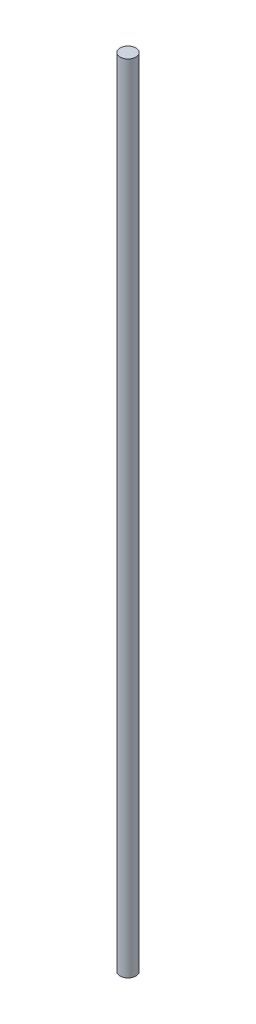
SolidWorks part; units mm, degrees
ref_plane "Front Plane" through (0, 0, 0) normal (0, 0, 1) x (1, 0, 0)
ref_plane "Top Plane" through (0, 0, 0) normal (0, 1, 0) x (1, 0, 0)
ref_plane "Right Plane" through (0, 0, 0) normal (1, 0, 0) x (0, 0, -1)
sketch "Sketch1" plane through (0, 0, 0) normal (0, 1, 0) x (1, 0, 0)
  circle A0 centre (0, 0) radius 2.5
  dimension "D1" = 5
extrude "Boss-Extrude1" add sketch "Sketch1" along normal blind 250
